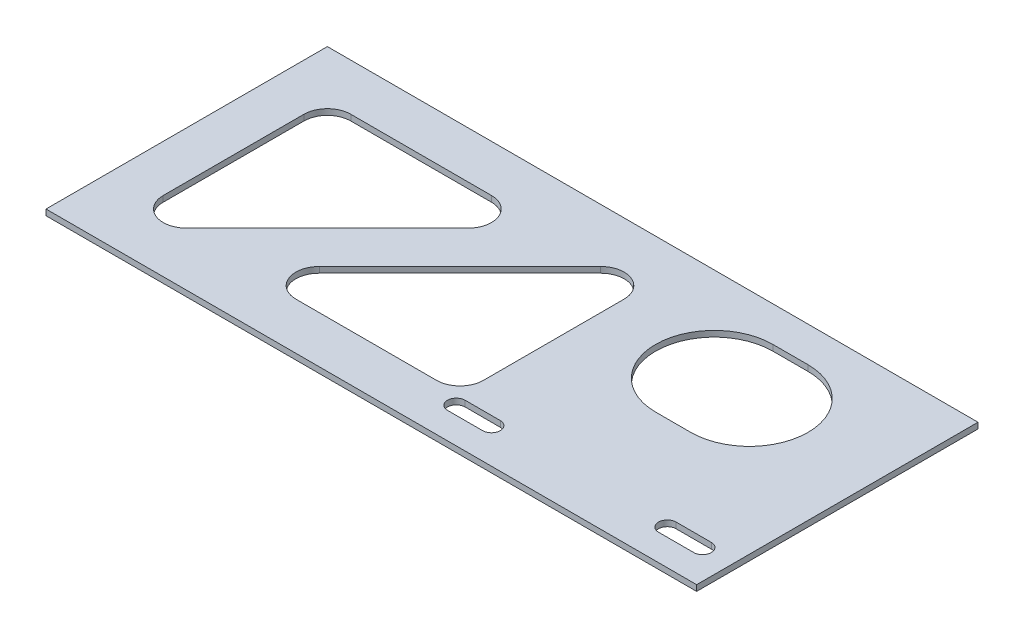
SolidWorks part; units mm, degrees
material "ASTM A36 Steel"
ref_plane "Front Plane" through (0, 0, 0) normal (0, 0, 1) x (1, 0, 0)
ref_plane "Top Plane" through (0, 0, 0) normal (0, 1, 0) x (1, 0, 0)
ref_plane "Right Plane" through (0, 0, 0) normal (1, 0, 0) x (0, 0, -1)
sketch "Sketch1" plane through (0, 0, 0) normal (0, 1, 0) x (1, 0, 0)
  line L1 (176.2125, 76.2) -> (-176.2125, 76.2)
  line L2 (176.2125, 76.2) -> (176.2125, -76.2)
  line L3 (176.2125, -76.2) -> (-176.2125, -76.2)
  line L4 (-176.2125, 76.2) -> (-176.2125, -76.2)
  line L5 (176.2125, 76.2) -> (-176.2125, -76.2) construction
  line L6 (176.2125, -76.2) -> (-176.2125, 76.2) construction
  point P0 (0, 0)
  dimension "D1" = 152.4
  dimension "D2" = 352.425
extrude "Boss-Extrude1" add sketch "Sketch1" along normal mid plane 3.175
sketch "Sketch2" plane through (0, 1.5875, 0) normal (0, 1, 0) x (1, 0, 0)
  line L0 (103.1875, 25.4) -> (84.1375, 25.4) construction
  line L1 (103.1875, -6.35) -> (84.1375, -6.35)
  line L2 (103.1875, 57.15) -> (84.1375, 57.15)
  line L4 (176.2125, -76.2) -> (176.2125, 76.2) construction
  line L5 (176.2125, 76.2) -> (-176.2125, 76.2) construction
  line L6 (-138.1125, 50.8) -> (-61.9125, 50.8)
  line L7 (-52.9322, 29.1197) -> (-129.1322, -47.0803)
  line L8 (-150.8125, -38.1) -> (-150.8125, 38.1)
  line L9 (-176.2125, 76.2) -> (-176.2125, -76.2) construction
  line L10 (-66.2705, -50.8) -> (9.9295, -50.8)
  line L11 (22.6295, -38.1) -> (22.6295, 38.1)
  line L12 (0.9493, 47.0803) -> (-75.2507, -29.1197)
  line L13 (-176.2125, -76.2) -> (176.2125, -76.2) construction
  line L14 (54.3795, -50.8) -> (144.4625, -50.8)
  line L15 (150.8125, -44.45) -> (150.8125, -38.1)
  line L16 (144.4625, -31.75) -> (54.3795, -31.75)
  line L17 (48.0295, -38.1) -> (48.0295, -44.45)
  arc A0 (103.1875, -6.35) -> (103.1875, 57.15) centre (103.1875, 25.4) ccw
  arc A1 (84.1375, 57.15) -> (84.1375, -6.35) centre (84.1375, 25.4) ccw
  arc A2 (-61.9125, 50.8) -> (-52.9322, 29.1197) centre (-61.9125, 38.1) cw
  arc A3 (-129.1322, -47.0803) -> (-150.8125, -38.1) centre (-138.1125, -38.1) cw
  arc A4 (-150.8125, 38.1) -> (-138.1125, 50.8) centre (-138.1125, 38.1) cw
  arc A5 (9.9295, -50.8) -> (22.6295, -38.1) centre (9.9295, -38.1) ccw
  arc A6 (22.6295, 38.1) -> (0.9493, 47.0803) centre (9.9295, 38.1) ccw
  arc A7 (-75.2507, -29.1197) -> (-66.2705, -50.8) centre (-66.2705, -38.1) ccw
  arc A8 (144.4625, -50.8) -> (150.8125, -44.45) centre (144.4625, -44.45) ccw
  arc A9 (150.8125, -38.1) -> (144.4625, -31.75) centre (144.4625, -38.1) ccw
  arc A10 (54.3795, -31.75) -> (48.0295, -38.1) centre (54.3795, -38.1) ccw
  arc A11 (48.0295, -44.45) -> (54.3795, -50.8) centre (54.3795, -44.45) ccw
  point P2 (93.6625, 25.4)
  point P31 (-138.1125, -50.8)
  point P32 (9.9295, 50.8)
  dimension "D2" = 31.75
  dimension "D7" = 12.7
  dimension "D9" = 25.4
  dimension "D14" = 6.35
  dimension "D1" = 19.05
  dimension "D3" = 19.05
  dimension "D4" = 82.55
  dimension "D5" = 25.4
  dimension "D6" = 25.4
  dimension "D8" = 45
  dimension "D10" = 25.4
  dimension "D11" = 25.4
  dimension "D12" = 25.4
  dimension "D13" = 25.4
extrude "Cut-Extrude1" cut sketch "Sketch2" against normal through all
sketch3d "TAG"
  line L0 (176.2125, 1.5875, 76.2) -> (176.2125, -1.5875, 76.2) construction
  line L1 (176.2125, 1.5875, 76.2) -> (176.2125, 1.5875, -76.2) construction
  line L2 (-176.2125, 1.5875, 76.2) -> (176.2125, 1.5875, 76.2) construction
  line L3 (176.2125, 1.5875, 76.2) -> (176.2125, -1.5875, 76.2)
  line L4 (176.2125, 1.5875, 76.2) -> (176.2125, 1.5875, -76.2)
  line L5 (-176.2125, 1.5875, 76.2) -> (176.2125, 1.5875, 76.2)
  dimension "D1" = 3.175
  dimension "D2" = 152.4
  dimension "D3" = 352.425
sketch "Sketch3" plane through (0, 1.5875, 0) normal (0, 1, 0) x (1, 0, 0)
  line L0 (160.3375, -57.15) -> (141.2875, -57.15) construction
  line L1 (160.3375, -61.9125) -> (141.2875, -61.9125)
  line L2 (160.3375, -52.3875) -> (141.2875, -52.3875)
  line L3 (46.0375, -57.15) -> (26.9875, -57.15) construction
  line L4 (46.0375, -61.9125) -> (26.9875, -61.9125)
  line L5 (46.0375, -52.3875) -> (26.9875, -52.3875)
  line L6 (176.2125, -76.2) -> (176.2125, 76.2) construction
  line L7 (-176.2125, -76.2) -> (176.2125, -76.2) construction
  arc A0 (160.3375, -61.9125) -> (160.3375, -52.3875) centre (160.3375, -57.15) ccw
  arc A1 (141.2875, -52.3875) -> (141.2875, -61.9125) centre (141.2875, -57.15) ccw
  arc A2 (46.0375, -61.9125) -> (46.0375, -52.3875) centre (46.0375, -57.15) ccw
  arc A3 (26.9875, -52.3875) -> (26.9875, -61.9125) centre (26.9875, -57.15) ccw
  point P2 (150.8125, -57.15)
  point P8 (36.5125, -57.15)
  dimension "D1" = 114.3
  dimension "D2" = 25.4
  dimension "D3" = 19.05
  dimension "D4" = 19.05
  dimension "D5" = 9.525
extrude "Cut-Extrude2" cut sketch "Sketch3" against normal through all
